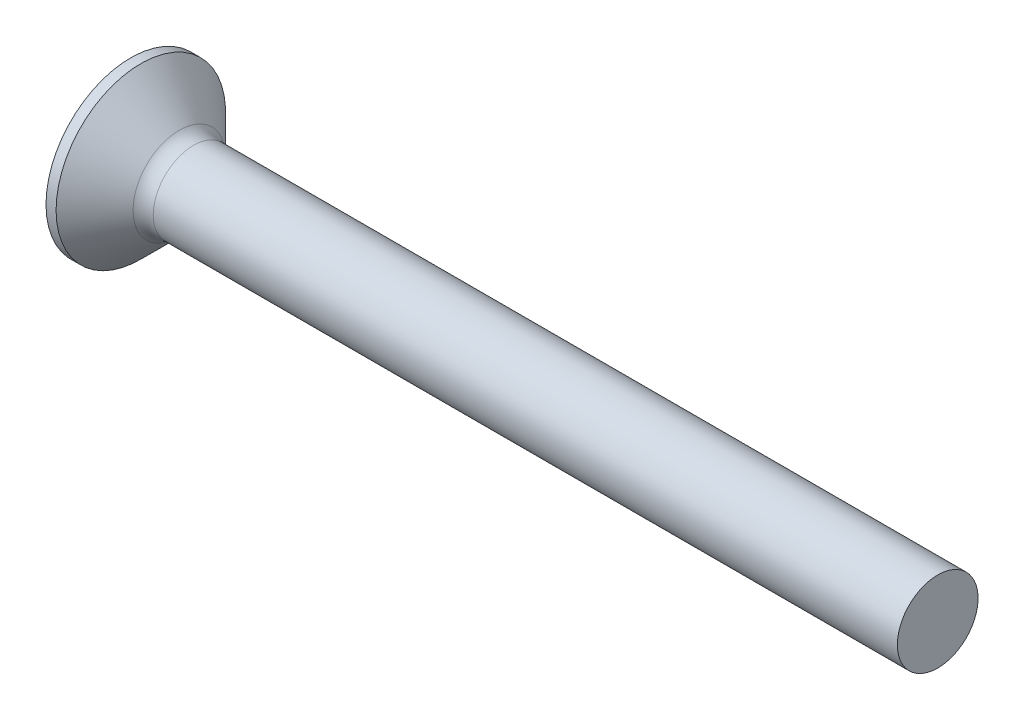
SolidWorks part; units mm, degrees
ref_plane "Plane1" through (0, 0, 0) normal (0, 0, 1) x (1, 0, 0)
ref_plane "Plane2" through (0, 0, 0) normal (0, 1, 0) x (1, 0, 0)
ref_plane "Plane3" through (0, 0, 0) normal (1, 0, 0) x (0, 0, -1)
sketch "BodySke" plane through (0, 0, 0) normal (0, 0, 1) x (1, 0, 0)
  line L0 (0, 0) -> (0, 4.2)
  line L1 (0, 4.2) -> (0.5, 4.2)
  line L2 (2.7, 2) -> (40, 2)
  line L3 (40, 2) -> (40, 0)
  line L4 (40, 0) -> (0, 0)
  line L5 (-6.35, 0) -> (82.55, 0) construction
  line L6 (2.7, -2) -> (40, -2) construction
  line L7 (0.5, -4.2) -> (2.7, -2) construction
  line L8 (0.5, 4.2) -> (2.7, 2)
  line L9 (0, -4.2) -> (0.5, -4.2) construction
  line L10 (3.4, 3.5875) -> (3.4, -5.9375) construction
  line L11 (24, 6.35) -> (24, -3.175) construction
  dimension "Diameter" = 4
  dimension "Length" = 40
  dimension "Head_ht" = 2.7
  dimension "Head_dia" = 8.4
  dimension "Head_ang" = 90
  dimension "D6" = 0.5
  dimension "Advance" = 0.7
  dimension "Thread_nom" = 16
revolve "Base-Revolve" add sketch "BodySke" angle 360 about L5
cosmetic thread "ThreadCosmetic" [suppressed] parameters "Thread_length"=16, "Thread_minor"=3.22
fillet "Fillet1" radius 1 1 edges at (2.7, 0, 2)
sketch "Sketch3" plane through (0, 0, 0) normal (-1, 0, 0) x (0, 0, 1)
  line L0 (-0.515, 2.2) -> (0.515, 2.2)
  line L1 (0.515, 2.2) -> (0.515, -2.2)
  line L2 (0.515, -2.2) -> (-0.515, -2.2)
  line L3 (-0.515, -2.2) -> (-0.515, 2.2)
  dimension "D1" = 2.2
  dimension "Cross_dia" = 4.4
  dimension "D2" = 0.515
  dimension "Cross_width" = 1.03
ref_plane "Plane4" through (2.51, 0, 0) normal (-1, 0, 0) x (0, 0, 1)
sketch "Sketch4" plane through (2.51, 0, 0) normal (-1, 0, 0) x (0, 0, 1)
  line L0 (-0.515, 0.9486) -> (0.515, 0.9486)
  line L3 (0.515, 0.9486) -> (0.515, -0.9486)
  line L4 (0.515, -0.9486) -> (-0.515, -0.9486)
  line L5 (-0.515, -0.9486) -> (-0.515, 0.9486)
  dimension "D1" = 1.03
  dimension "D2" = 1.8971
  dimension "D3" = 0.515
  dimension "D4" = 0.9486
loft "Recess" cut profiles "Sketch3", "Sketch4"
pattern_circular "RecPat" count 2 every 90 about axis through (0, 0, 0) along (1, 0, 0) of "Recess"
sketch "RecCorSke" plane through (0, 0, 0) normal (0, 0, 1) x (1, 0, 0)
  line L0 (-3.175, 0) -> (15.875, 0) construction
  line L2 (0, 0) -> (0, 1.0265)
  line L3 (0, 1.0265) -> (2.51, 0.851)
  line L4 (2.51, 0.851) -> (2.7865, 0)
  line L5 (2.7865, 0) -> (0, 0)
  dimension "Diameter" = 1.702
  dimension "Depth" = 2.51
  dimension "Draft_angle" = 4
  dimension "Bottom_angle" = 18
revolve "RecessCore" cut sketch "RecCorSke" angle 360 about L0
sketch "ThdSchSke" plane through (0, 0, 0) normal (0, 0, 1) x (1, 0, 0)
  line L0 (24, -1.61) -> (23.7269, -2)
  line L1 (24, -1.61) -> (24.2731, -2)
  line L2 (24.2731, -2) -> (24.2731, -2.5)
  line L3 (-3.175, 0) -> (5.1513, 0) construction
  line L5 (24.2731, -2.5) -> (23.7269, -2.5)
  line L6 (23.7269, -2.5) -> (23.7269, -2)
  line L7 (0, 4.2) -> (0, -4.2) construction
  dimension "Thread_minor" = 3.22
  dimension "Diameter" = 4
  dimension "Start" = 24
  dimension "SideAngle" = 55
  dimension "VeeAngle" = 70
  dimension "Overcut" = 5
revolve "ThreadSchematic" [suppressed] cut sketch "ThdSchSke" angle 360 about L3
pattern_linear "ThdSchPat" [suppressed]
equation "\"D1@Sketch3\" = \"Cross_dia@Sketch3\" / 2"
equation "\"D2@Sketch3\" = \"Cross_width@Sketch3\" / 2"
equation "\"Depth@RecCorSke\" = \"Cross_depth@Plane4\""
equation "\"D1@Sketch4\" = \"Cross_width@Sketch3\""
equation "\"D2@Sketch4\" = \"Cross_dia@Sketch3\" - 2.0 * \"Cross_depth@Plane4\" * tan(26.5  * 0.017453292)"
equation "\"D3@Sketch4\" = \"D1@Sketch4\" / 2"
equation "\"D4@Sketch4\" = \"D2@Sketch4\" / 2"
equation "\"Thread_length@ThreadCosmetic\" = ((sgn( (\"Length@BodySke\" - \"Advance@BodySke\" * 1.0 - \"Head_ht@BodySke\" ) - \"Thread_nom@BodySke\" )-1)*( (\"Length@BodySke\" - \"Advance@BodySke\" * 1.0 - \"Head_ht@BodySke\" ) - \"Thread_nom@BodySke\" ))/-2+ \"Thread_nom@BodySke\""
equation "\"Thread_minor@ThdSchSke\" = \"Thread_minor@ThreadCosmetic\""
equation "\"Diameter@ThdSchSke\" = \"Diameter@BodySke\""
equation "\"Overcut@ThdSchSke\" = \"Diameter@BodySke\" * 1.25"
equation "\"Start@ThdSchSke\" = 0.000001 + \"Length@BodySke\" - \"Thread_length@ThreadCosmetic\"  '---Countersunk---"
equation "\"Num_threads@ThdSchPat\" = int( \"Thread_length@ThreadCosmetic\" / \"Advance@BodySke\" + 0.999 )  + 1"
equation "\"Advance@ThdSchPat\" = \"Thread_length@ThreadCosmetic\" /  (\"Num_threads@ThdSchPat\" - 1) 'relax it"
